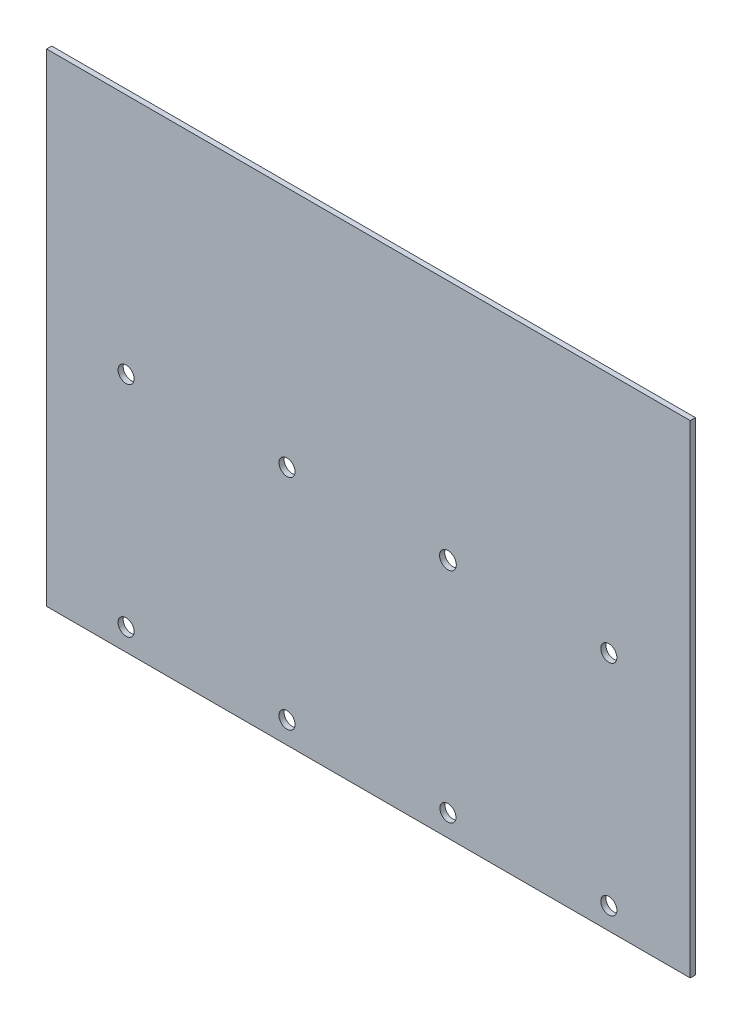
SolidWorks part; units mm, degrees
ref_plane "Plan de face" through (0, 0, 0) normal (0, 0, 1) x (1, 0, 0)
ref_plane "Plan de dessus" through (0, 0, 0) normal (0, 1, 0) x (1, 0, 0)
ref_plane "Plan de droite" through (0, 0, 0) normal (1, 0, 0) x (0, 0, -1)
sketch "Esquisse1" plane through (0, 0, 0) normal (0, 0, 1) x (1, 0, 0)
  line L1 (-100, -75) -> (100, -75)
  line L2 (-100, -75) -> (-100, 75)
  line L3 (-100, 75) -> (100, 75)
  line L4 (100, -75) -> (100, 75)
  line L5 (-100, -75) -> (100, 75) construction
  line L6 (-100, 75) -> (100, -75) construction
  point P0 (0, 0)
  dimension "D1" = 200
  dimension "D2" = 150
extrude "Boss.-Extru.1" add sketch "Esquisse1" along normal blind 1.6
sketch "Esquisse2" plane through (0, 0, 0) normal (0, 0, -1) x (-1, 0, 0)
  circle A0 centre (75.3, -0.1966) radius 2.5
  circle A1 centre (25.3, -0.1966) radius 2.5
  circle A2 centre (-24.7, -0.1966) radius 2.6
  circle A3 centre (-74.7, -0.1966) radius 2.5
  circle A4 centre (75.3, -68.1966) radius 2.5
  circle A5 centre (25.3, -68.1966) radius 2.5
  circle A6 centre (-24.7, -68.1966) radius 2.5
  circle A7 centre (-74.7, -68.1966) radius 2.5
extrude "Enlèv. mat.-Extru.1" cut sketch "Esquisse2" against normal blind 10
